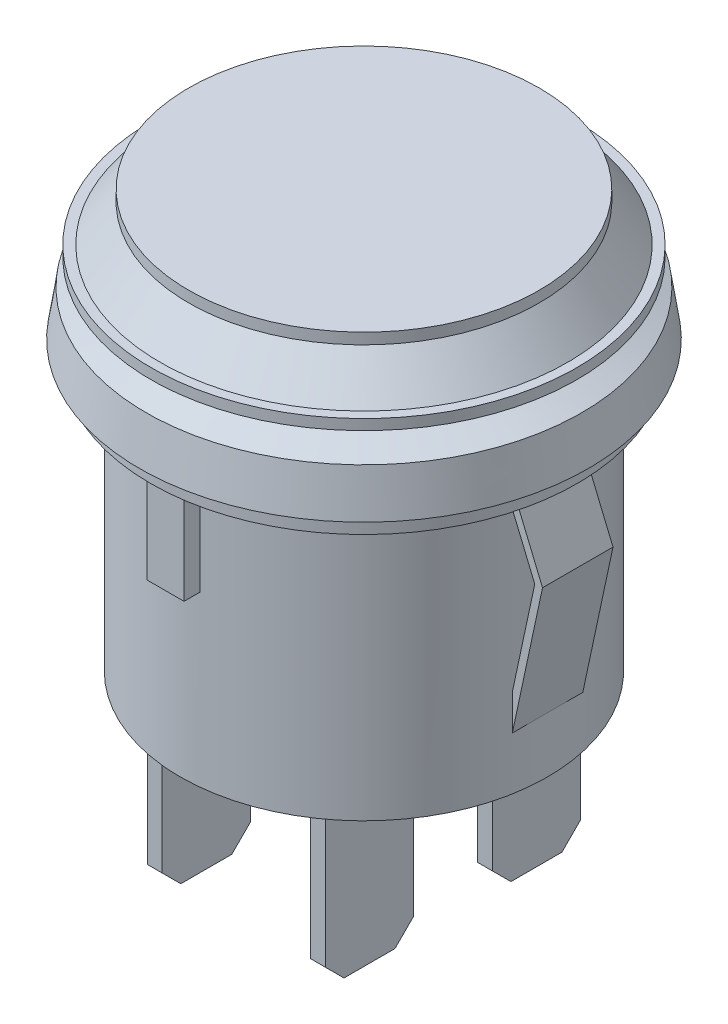
SolidWorks part; units mm, degrees
ref_plane "Front Plane" through (0, 0, 0) normal (0, 0, 1) x (1, 0, 0)
ref_plane "Top Plane" through (0, 0, 0) normal (0, 1, 0) x (1, 0, 0)
ref_plane "Right Plane" through (0, 0, 0) normal (1, 0, 0) x (0, 0, -1)
sketch "Sketch1" plane through (0, 0, 0) normal (0, 1, 0) x (1, 0, 0)
  circle A0 centre (0, 0) radius 9.9
  dimension "D1" = 19.8
extrude "Boss-Extrude1" add sketch "Sketch1" along normal blind 14.5
sketch "Sketch2" plane through (0, 14.5, 0) normal (0, 1, 0) x (1, 0, 0)
  circle A0 centre (0, 0) radius 11.5
  dimension "D1" = 23
extrude "Boss-Extrude2" add sketch "Sketch2" along normal blind 1
ref_plane "Plane1" through (0, 0, 10.7) normal (0, 0, 1) x (1, 0, 0)
sketch "Sketch3" plane through (0, 0, 10.7) normal (0, 0, 1) x (1, 0, 0)
  line L0 (0, 0) -> (0, 17.4901) construction
  line L1 (-9.9, 14.5) -> (9.9, 14.5) construction
  line L2 (-1, 14.5) -> (1, 14.5)
  line L3 (-1, 14.5) -> (-1, 9.1)
  line L4 (-1, 9.1) -> (1, 9.1)
  line L5 (1, 14.5) -> (1, 9.1)
  dimension "D1" = 2
  dimension "D2" = 5.4
extrude "Boss-Extrude3" add sketch "Sketch3" against normal up to surface (0.8506 mm away)
sketch "Sketch4" plane through (0, 0, 0) normal (0, 0, 1) x (1, 0, 0)
  line L0 (-9.9, 14.5) -> (-11.5287, 10.6)
  line L1 (-11.5287, 10.6) -> (-9.9, 3)
  line L2 (-9.9, 14.5) -> (-9.9, 0) construction
  line L3 (-9.9, 13.462) -> (-11.1113, 10.5614)
  line L4 (-11.1113, 10.5614) -> (-9.9, 4.9089)
  line L5 (-9.9, 3) -> (-9.9, 4.9089)
  line L6 (-11.1113, 10.5614) -> (-9.5089, 3.0838) construction
  line L7 (-9.9, 13.462) -> (-9.9, 14.5)
  line L8 (-9.5309, 14.3459) -> (-11.1113, 10.5614) construction
  line L9 (-11.5, 14.5) -> (11.5, 14.5) construction
  line L11 (0, 0) -> (0, 18.7514) construction
  line L12 (-9.9, 0) -> (9.9, 0) construction
  line L13 (9.9, 13.462) -> (9.9, 14.5)
  line L14 (9.9, 3) -> (9.9, 4.9089)
  line L15 (11.1113, 10.5614) -> (9.9, 4.9089)
  line L16 (9.9, 13.462) -> (11.1113, 10.5614)
  line L17 (11.5287, 10.6) -> (9.9, 3)
  line L18 (9.9, 14.5) -> (11.5287, 10.6)
  dimension "D2" = 7.6
  dimension "D3" = 3.9
  dimension "D1" = 0.4
extrude "Boss-Extrude4" add sketch "Sketch4" along normal mid plane 3.8 separate body
sketch "Sketch5" plane through (0, 0, 0) normal (0, 0, 1) x (1, 0, 0)
  line L0 (-12.1, 15.5) -> (0, 15.5)
  line L1 (11.5, 15.5) -> (-11.5, 15.5) construction
  line L2 (-12.1, 15.5) -> (-11.7419, 17.9258)
  line L3 (0, 0) -> (0, 26.4802) construction
  line L4 (-11.7419, 17.9258) -> (-9.45, 18.9385)
  line L5 (-9.45, 22.5) -> (0, 22.5)
  line L6 (-9.45, 18.9385) -> (-11.4828, 19.3389)
  line L7 (-11.4828, 19.3389) -> (-11.4828, 19.9041)
  line L8 (-11.4828, 19.9041) -> (-10.9882, 19.9041)
  line L9 (-10.9882, 19.9041) -> (-9.45, 21.9061)
  line L10 (-9.45, 21.9061) -> (-9.45, 22.5)
  line L11 (0, 15.5) -> (0, 22.5)
  dimension "D3" = 7
revolve "Revolve1" add sketch "Sketch5" angle 360 about L3
sketch "Sketch6" plane through (0, 0, 0) normal (0, -1, 0) x (1, 0, 0)
  line L0 (0, 0) -> (0, 12.8375) construction
  line L1 (0, 0) -> (16.9065, 0) construction
  line L3 (-4.8, 6.875) -> (-4, 6.875)
  line L4 (-4.8, 6.875) -> (-4.8, 2.125)
  line L5 (-4.8, 2.125) -> (-4, 2.125)
  line L6 (-4, 6.875) -> (-4, 2.125)
  line L7 (-4.8, -2.125) -> (-4, -2.125)
  line L8 (-4.8, -2.125) -> (-4.8, -6.875)
  line L9 (-4.8, -6.875) -> (-4, -6.875)
  line L10 (-4, -2.125) -> (-4, -6.875)
  line L11 (4, 6.875) -> (4.8, 6.875)
  line L12 (4, 6.875) -> (4, 2.125)
  line L13 (4, 2.125) -> (4.8, 2.125)
  line L14 (4.8, 6.875) -> (4.8, 2.125)
  line L15 (4, -2.125) -> (4.8, -2.125)
  line L16 (4, -2.125) -> (4, -6.875)
  line L17 (4, -6.875) -> (4.8, -6.875)
  line L18 (4.8, -2.125) -> (4.8, -6.875)
  dimension "D1" = 4.75
  dimension "D2" = 0.8
  dimension "D3" = 4.25
  dimension "D4" = 8
extrude "Boss-Extrude5" add sketch "Sketch6" along normal blind 9
chamfer "Chamfer1" distance 1 angle 45 8 edges at (-4.4, -9, 6.875) (-4.4, -9, 2.125) (-4.4, -9, -2.125) (-4.4, -9, -6.875) (4.4, -9, -6.875) (4.4, -9, -2.125) (4.4, -9, 2.125) (4.4, -9, 6.875)
